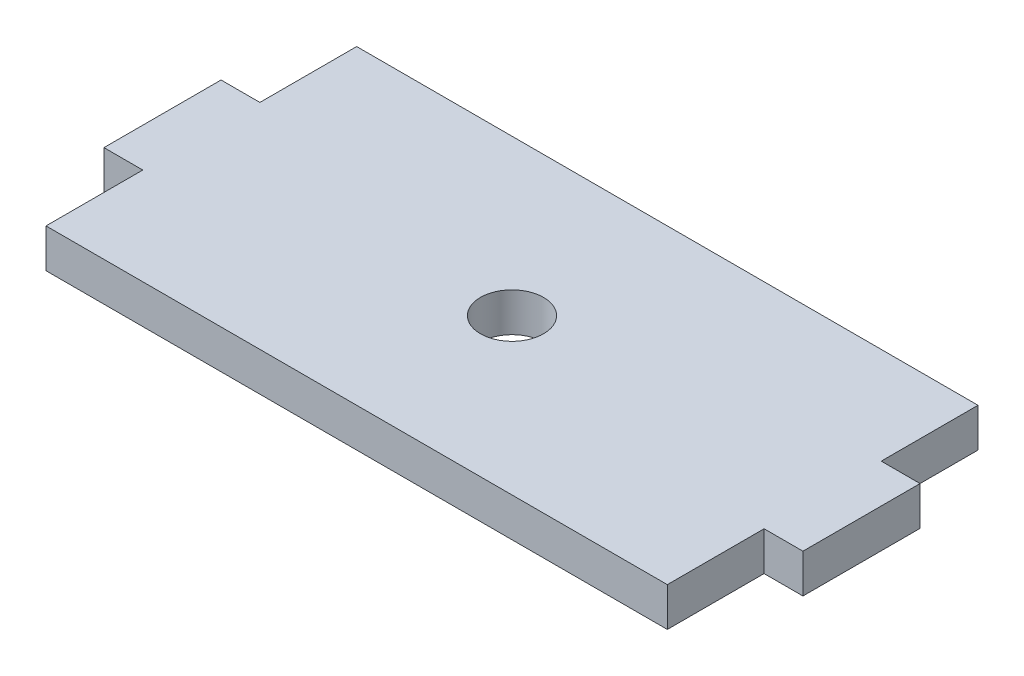
SolidWorks part; units mm, degrees
ref_plane "Front Plane" through (0, 0, 0) normal (0, 0, 1) x (1, 0, 0)
ref_plane "Top Plane" through (0, 0, 0) normal (0, 1, 0) x (1, 0, 0)
ref_plane "Right Plane" through (0, 0, 0) normal (1, 0, 0) x (0, 0, -1)
sketch "Sketch1" plane through (0, 0, 0) normal (0, 1, 0) x (1, 0, 0)
  line L0 (-25.4, -4.7879) -> (-25.4, -12.7)
  line L1 (-25.4, 12.7) -> (25.4, 12.7)
  line L2 (-25.4, 12.7) -> (-25.4, 4.7879)
  line L3 (-25.4, -12.7) -> (25.4, -12.7)
  line L4 (25.4, 12.7) -> (25.4, 4.7879)
  line L5 (-25.4, 12.7) -> (25.4, -12.7) construction
  line L6 (-25.4, -12.7) -> (25.4, 12.7) construction
  line L7 (25.4, 4.7879) -> (28.575, 4.7879)
  line L9 (25.4, -4.7879) -> (28.575, -4.7879)
  line L10 (28.575, 4.7879) -> (28.575, -4.7879)
  line L11 (-28.575, 0) -> (28.575, 0) construction
  line L13 (-28.575, 4.7879) -> (-25.4, 4.7879)
  line L14 (-28.575, 4.7879) -> (-28.575, -4.7879)
  line L15 (-28.575, -4.7879) -> (-25.4, -4.7879)
  line L19 (25.4, -4.7879) -> (25.4, -12.7)
  circle A0 centre (0, 0) radius 2.5797
  point P0 (0, 0)
  dimension "D6" = 5.1594
  dimension "D1" = 25.4
  dimension "D2" = 3.175
  dimension "D3" = 9.5758
  dimension "D4" = 50.8
  dimension "D5" = 3.175
extrude "Boss-Extrude1" add sketch "Sketch1" along normal mid plane 3.175 contours L19 L9 L10 L7 L4 L1 L2 L13 L14 L15 L0 L3 A0
equation "\"D3@Sketch1\"=0.375in+0.002in"
